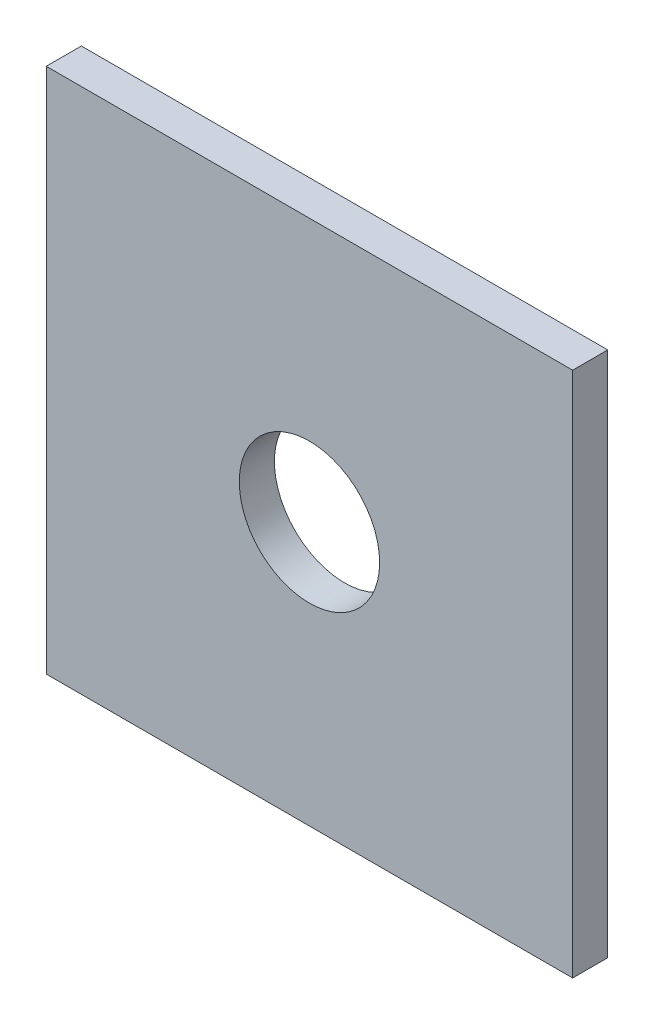
SolidWorks part; units mm, degrees
ref_plane "Front Plane" through (0, 0, 0) normal (0, 0, 1) x (1, 0, 0)
ref_plane "Top Plane" through (0, 0, 0) normal (0, 1, 0) x (1, 0, 0)
ref_plane "Right Plane" through (0, 0, 0) normal (1, 0, 0) x (0, 0, -1)
sketch "Sketch1" plane through (0, 0, 0) normal (0, 0, 1) x (1, 0, 0)
  line L1 (-11.9063, -11.9063) -> (11.9062, -11.9062)
  line L2 (-11.9063, -11.9063) -> (-11.9063, 11.9062)
  line L3 (-11.9063, 11.9062) -> (11.9062, 11.9062)
  line L4 (11.9062, -11.9062) -> (11.9062, 11.9062)
  line L5 (-11.9063, -11.9063) -> (11.9062, 11.9062) construction
  line L6 (-11.9063, 11.9062) -> (11.9062, -11.9062) construction
  circle A0 centre (0, 0) radius 3.175
  dimension "D1" = 6.35
  dimension "D2" = 23.8125
  dimension "D3" = 23.8125
extrude "Boss-Extrude1" add sketch "Sketch1" along normal blind 1.5875
